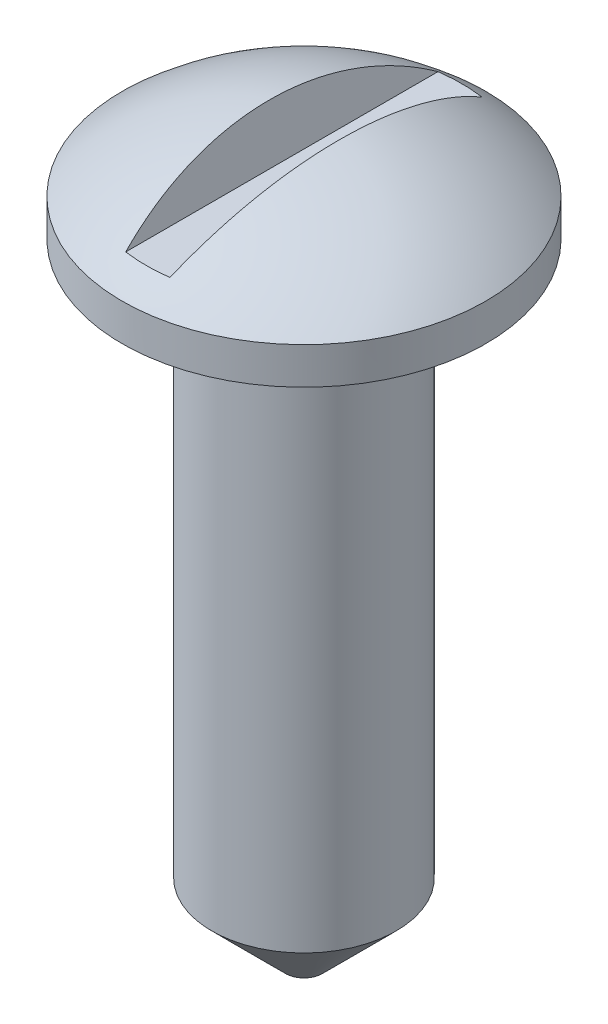
SolidWorks part; units mm, degrees
ref_plane "Front Plane" through (0, 0, 0) normal (0, 0, 1) x (1, 0, 0)
ref_plane "Top Plane" through (0, 0, 0) normal (0, 1, 0) x (1, 0, 0)
ref_plane "Right Plane" through (0, 0, 0) normal (1, 0, 0) x (0, 0, -1)
sketch "Sketch1" plane through (0, 0, 0) normal (0, 0, 1) x (1, 0, 0)
  line L0 (0, -10.1362) -> (0, 60.8169) construction
  line L1 (6.35, 0) -> (-6.35, 0)
  line L2 (-6.35, 0) -> (-6.35, 43.18)
  line L3 (-6.35, 43.18) -> (-12.5178, 43.18)
  line L5 (-12.5178, 45.72) -> (12.5178, 45.72)
  line L6 (0, 45.72) -> (0, 0)
  line L11 (-12.5178, 43.18) -> (-12.5178, 45.72)
  line L12 (12.5178, 43.18) -> (12.5178, 45.72)
  line L13 (6.35, 43.18) -> (12.5178, 43.18)
  line L14 (6.35, 0) -> (6.35, 43.18)
  arc A1 (-12.5178, 45.72) -> (12.5178, 45.72) centre (0, 31.3601) cw
  point P14 (0, 0)
  point P15 (0, 50.4101)
  dimension "D4" = 19.05
  dimension "D5" = 50.4101
  dimension "D1" = 43.18
  dimension "D2" = 6.35
  dimension "D3" = 2.54
other "AlignGroup1"
revolve "Revolve13" add sketch "Sketch1" angle 360 about L0
chamfer "Chamfer4" distance 5.08 angle 45 1 edges at (0, 0, -6.35)
sketch "Sketch4" plane through (0, 0, 0) normal (0, 0, 1) x (1, 0, 0)
  line L0 (0, 45.72) -> (0, 58.7847) construction
  line L1 (12.5178, 45.72) -> (-12.5178, 45.72) construction
  line L2 (-2.3926, 50.2592) -> (-1.5226, 47.0123)
  line L3 (-1.5226, 47.0123) -> (1.5226, 47.0123)
  line L4 (2.3926, 50.2592) -> (1.5226, 47.0123)
  arc A0 (12.5178, 45.72) -> (-12.5178, 45.72) centre (0, 31.3601) ccw construction
  point P13 (0, 47.0123)
  dimension "D1" = 1.2923
  dimension "D2" = 15
extrude "Cut-Extrude2" cut sketch "Sketch4" against normal through all and the other way through all flip side to cut
